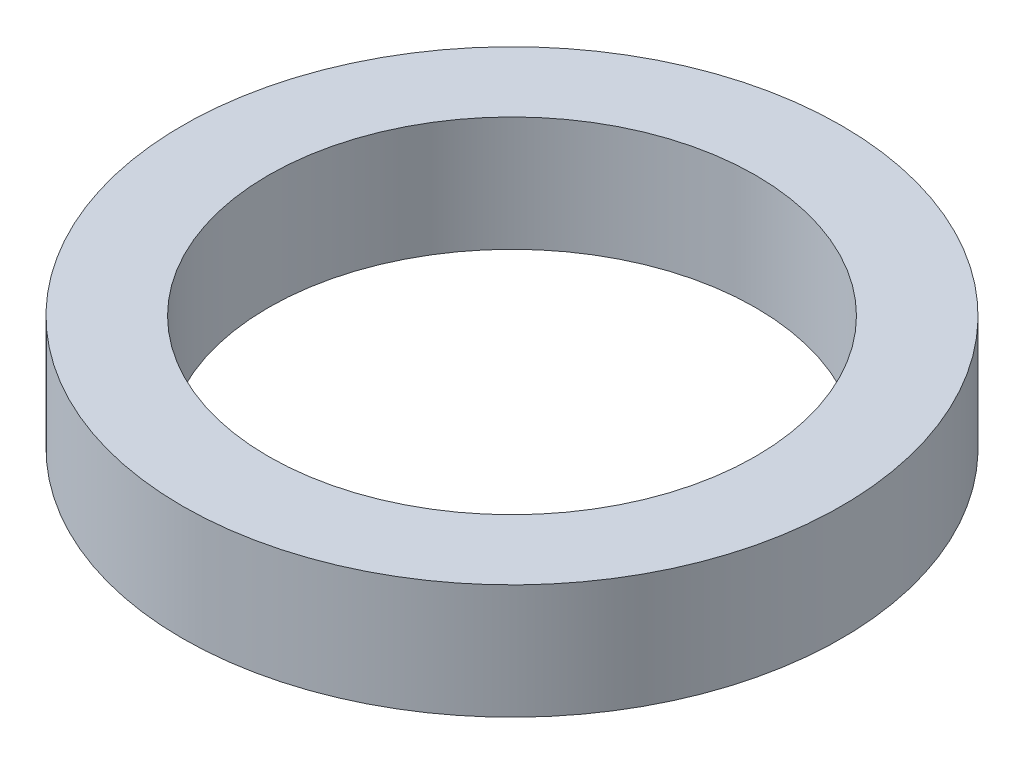
SolidWorks part; units mm, degrees
ref_plane "Front Plane" through (0, 0, 0) normal (0, 0, 1) x (1, 0, 0)
ref_plane "Top Plane" through (0, 0, 0) normal (0, 1, 0) x (1, 0, 0)
ref_plane "Right Plane" through (0, 0, 0) normal (1, 0, 0) x (0, 0, -1)
sketch "Sketch1" plane through (0, 0, 0) normal (0, 1, 0) x (1, 0, 0)
  circle A0 centre (0, 0) radius 8.5
  circle A1 centre (0, 0) radius 11.5
  dimension "D1" = 17
  dimension "D2" = 23
extrude "Boss-Extrude1" add sketch "Sketch1" along normal blind 4
